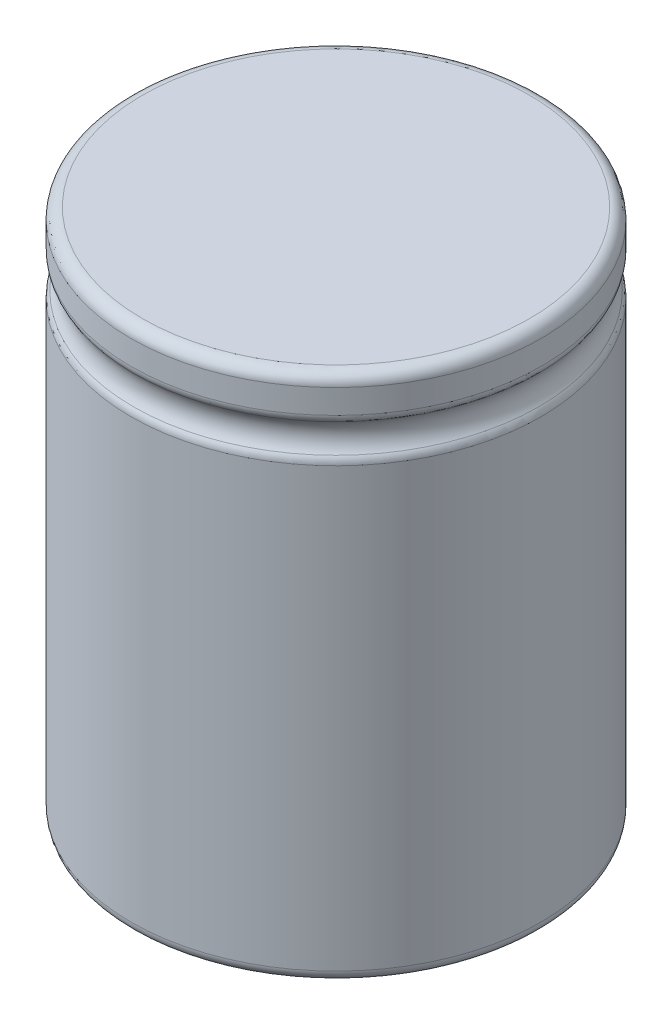
SolidWorks part; units mm, degrees
ref_plane "Plano frontal" through (0, 0, 0) normal (0, 0, 1) x (1, 0, 0)
ref_plane "Plano superior" through (0, 0, 0) normal (0, 1, 0) x (1, 0, 0)
ref_plane "Plano direito" through (0, 0, 0) normal (1, 0, 0) x (0, 0, -1)
sketch "Esboço1" plane through (0, 0, 0) normal (0, 1, 0) x (1, 0, 0)
  circle A0 centre (0, 0) radius 17.85
  dimension "D1" = 35.7
extrude "Ressalto-extrusão1" add sketch "Esboço1" along normal blind 46
sketch "Esboço2" plane through (0, 0, 0) normal (0, 0, 1) x (1, 0, 0)
  line L0 (17.85, 46) -> (-17.85, 46) construction
  line L1 (-17.85, 0) -> (17.85, 0) construction
  line L2 (17.85, 46) -> (0, 46) construction
  line L3 (0, 0) -> (17.85, 0) construction
  line L4 (17.85, 46) -> (17.85, 0) construction
  line L5 (0, 46) -> (0, 0) construction
  line L6 (0, 41) -> (17.85, 41) construction
  line L7 (17.85, 42.5) -> (17.85, 39.5) construction
  line L8 (17.85, 0) -> (17.85, 46) construction
  line L9 (17.85, 42.5) -> (17.85, 39.5)
  arc A0 (17.85, 42.5) -> (17.85, 39.5) centre (19.1729, 41) ccw
  dimension "D2" = 2
  dimension "D1" = 5
  dimension "D3" = 1.5
sweep "Varredura de corte1" cut profiles "Esboço2" path edge at (0, 46, 17.85)
fillet "Filete1" radius 1 2 edges at (0, 0, 17.85) (0, 46, 17.85)
fillet "Filete2" radius 1 2 edges at (0, 39.5, -17.85) (0, 42.5, -17.85)
